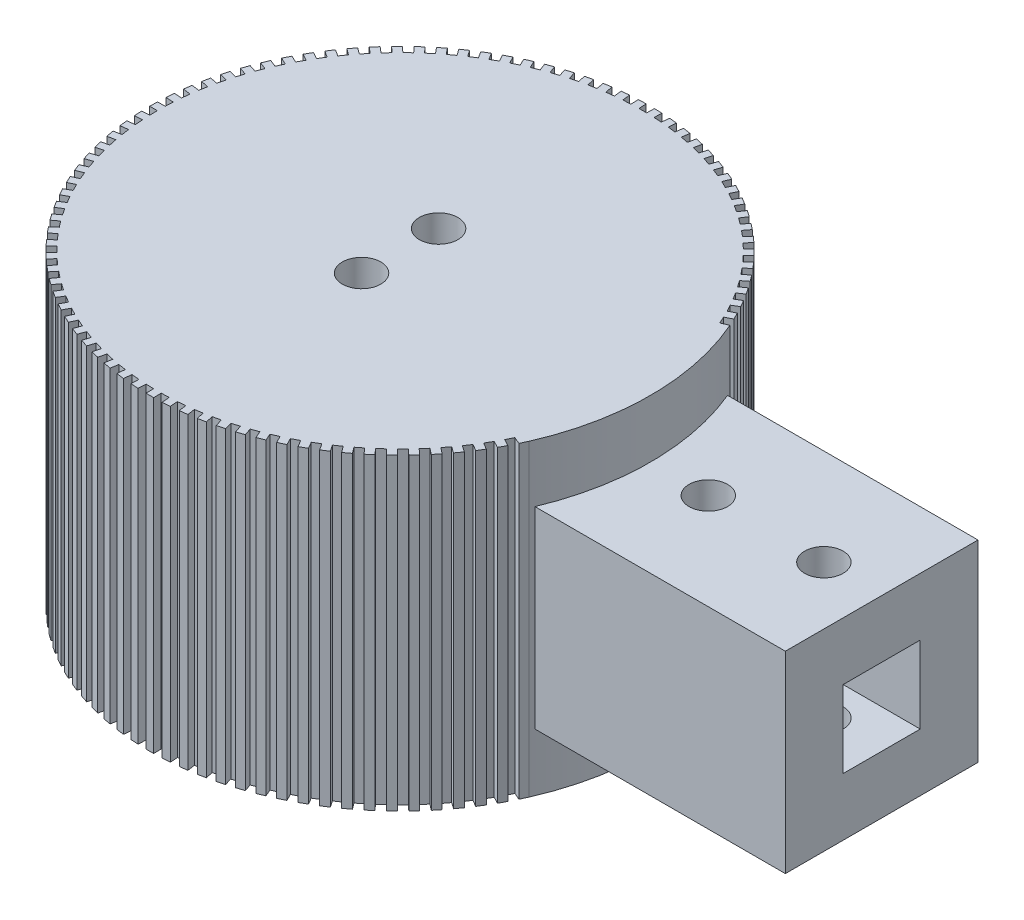
SolidWorks part; units mm, degrees
ref_plane "Front Plane" through (0, 0, 0) normal (0, 0, 1) x (1, 0, 0)
ref_plane "Top Plane" through (0, 0, 0) normal (0, 1, 0) x (1, 0, 0)
ref_plane "Right Plane" through (0, 0, 0) normal (1, 0, 0) x (0, 0, -1)
sketch "Sketch1" plane through (0, 0, 0) normal (0, 1, 0) x (1, 0, 0)
  circle A0 centre (0, 0) radius 32.5
  dimension "D1" = 65
extrude "Boss-Extrude1" add sketch "Sketch1" along normal blind 40
sketch "Sketch2" plane through (0, 0, 0) normal (1, 0, 0) x (0, 0, -1)
  line L0 (0, 0) -> (0, 40) construction
  line L1 (32.5, 40) -> (-32.5, 40) construction
  line L2 (12.5, 20) -> (-12.5, 20) construction
  line L3 (0, 32.5) -> (0, 7.5) construction
  line L4 (0, 32.5) -> (-12.5, 32.5)
  line L5 (-12.5, 32.5) -> (-12.5, 7.5)
  line L6 (-12.5, 7.5) -> (12.5, 7.5)
  line L7 (12.5, 7.5) -> (12.5, 32.5)
  line L8 (12.5, 32.5) -> (0, 32.5)
  line L10 (5, 15) -> (-5, 15)
  line L11 (5, 15) -> (5, 25)
  line L12 (5, 25) -> (-5, 25)
  line L13 (-5, 15) -> (-5, 25)
  line L14 (5, 15) -> (-5, 25) construction
  line L15 (5, 25) -> (-5, 15) construction
  point P8 (0, 20)
  point P11 (0, 20)
  point P15 (0, 20)
  dimension "D1" = 25
  dimension "D2" = 25
  dimension "D3" = 10
  dimension "D4" = 10
extrude "Boss-Extrude2" add sketch "Sketch2" along normal blind 62.5
sketch "Sketch3" plane through (0, 40, 0) normal (0, 1, 0) x (1, 0, 0)
  line L0 (0, -5) -> (0, 5) construction
  circle A0 centre (0, 5) radius 2.5
  circle A1 centre (0, -5) radius 2.5
  point P4 (0, 0)
  dimension "D2" = 5
  dimension "D3" = 5
  dimension "D1" = 10
extrude "Cut-Extrude1" cut sketch "Sketch3" against normal through all both and the other way through all
sketch "Sketch4" plane through (0, 32.5, 0) normal (0, 1, 0) x (1, 0, 0)
  line L1 (62.5, 12.5) -> (62.5, -12.5) construction
  line L2 (32.5, 0) -> (47.5, 0) construction
  line L3 (47.5, 0) -> (62.5, 0) construction
  arc A0 (30, -12.5) -> (30, 12.5) centre (0, 0) ccw construction
  circle A1 centre (40, 0) radius 2.5
  circle A2 centre (55, 0) radius 2.5
  dimension "D1" = 5
  dimension "D2" = 5
extrude "Cut-Extrude2" cut sketch "Sketch4" against normal through all both and the other way through all
sketch "Sketch5" plane through (0, 40, 0) normal (0, 1, 0) x (1, 0, 0)
  line L0 (-31.5, 0) -> (-32.4949, 0)
  line L1 (-32.4949, 0) -> (-32.4795, 1)
  line L2 (-32.4795, 1) -> (-31.4841, 1)
  line L3 (-31.4366, 1.9979) -> (-32.4294, 2.061)
  line L4 (-32.4294, 2.061) -> (-32.3507, 3.058)
  line L5 (-32.3507, 3.058) -> (-31.3573, 2.9948)
  line L6 (-31.2466, 3.9877) -> (-32.2334, 4.1136)
  line L7 (-32.2334, 4.1136) -> (-32.0916, 5.1036)
  line L8 (-32.0916, 5.1036) -> (-31.1042, 4.9776)
  line L9 (-30.9308, 5.9614) -> (-31.9076, 6.1497)
  line L10 (-31.9076, 6.1497) -> (-31.7033, 7.1287)
  line L11 (-31.7033, 7.1287) -> (-30.7259, 6.9403)
  line L12 (-30.4904, 7.9112) -> (-31.4534, 8.161)
  line L13 (-31.4534, 8.161) -> (-31.1873, 9.1251)
  line L14 (-31.1873, 9.1251) -> (-30.2239, 8.8751)
  line L15 (-29.9272, 9.8291) -> (-30.8724, 10.1395)
  line L16 (-30.8724, 10.1395) -> (-30.5458, 11.0848)
  line L17 (-30.5458, 11.0848) -> (-29.6001, 10.7742)
  line L18 (-29.2436, 11.7074) -> (-30.1672, 12.0771)
  line L19 (-30.1672, 12.0771) -> (-29.7812, 12.9998)
  line L20 (-29.7812, 12.9998) -> (-28.8572, 12.6298)
  line L21 (-28.4422, 13.5385) -> (-29.3405, 13.9661)
  line L22 (-29.3405, 13.9661) -> (-28.8968, 14.8624)
  line L23 (-28.8968, 14.8624) -> (-27.9981, 14.4346)
  line L24 (-27.5263, 15.3152) -> (-28.3956, 15.7989)
  line L25 (-28.3956, 15.7989) -> (-27.896, 16.6653)
  line L26 (-27.896, 16.6653) -> (-27.0262, 16.1813)
  line L27 (-26.4995, 17.0302) -> (-27.3364, 17.5681)
  line L28 (-27.3364, 17.5681) -> (-26.7828, 18.401)
  line L29 (-26.7828, 18.401) -> (-25.9455, 17.8629)
  line L30 (-25.366, 18.6766) -> (-26.1671, 19.2665)
  line L31 (-26.1671, 19.2665) -> (-25.5618, 20.0626)
  line L32 (-25.5618, 20.0626) -> (-24.7603, 19.4725)
  line L33 (-24.1304, 20.2478) -> (-24.8925, 20.8873)
  line L34 (-24.8925, 20.8873) -> (-24.2379, 21.6434)
  line L35 (-24.2379, 21.6434) -> (-23.4754, 21.0036)
  line L36 (-22.7976, 21.7375) -> (-23.5176, 22.424)
  line L37 (-23.5176, 22.424) -> (-22.8164, 23.1371)
  line L38 (-22.8164, 23.1371) -> (-22.0961, 22.4503)
  line L39 (-21.373, 23.1396) -> (-22.0481, 23.8705)
  line L40 (-22.0481, 23.8705) -> (-21.303, 24.5377)
  line L41 (-21.303, 24.5377) -> (-20.6277, 23.8065)
  line L42 (-19.8624, 24.4486) -> (-20.4897, 25.2208)
  line L43 (-20.4897, 25.2208) -> (-19.7039, 25.8394)
  line L44 (-19.7039, 25.8394) -> (-19.0763, 25.0668)
  line L45 (-18.2718, 25.6591) -> (-18.8489, 26.4695)
  line L46 (-18.8489, 26.4695) -> (-18.0254, 27.0371)
  line L47 (-18.0254, 27.0371) -> (-17.448, 26.2263)
  line L48 (-16.6076, 26.7664) -> (-17.1321, 27.6117)
  line L49 (-17.1321, 27.6117) -> (-16.2743, 28.1259)
  line L50 (-16.2743, 28.1259) -> (-15.7495, 27.2801)
  line L51 (-14.8765, 27.7658) -> (-15.3464, 28.6427)
  line L52 (-15.3464, 28.6427) -> (-14.4577, 29.1014)
  line L53 (-14.4577, 29.1014) -> (-13.9876, 28.2241)
  line L54 (-13.0856, 28.6534) -> (-13.4989, 29.5584)
  line L55 (-13.4989, 29.5584) -> (-12.5828, 29.9598)
  line L56 (-12.5828, 29.9598) -> (-12.1693, 29.0544)
  line L57 (-11.2419, 29.4257) -> (-11.597, 30.355)
  line L58 (-11.597, 30.355) -> (-10.6573, 30.6975)
  line L59 (-10.6573, 30.6975) -> (-10.3021, 29.7677)
  line L60 (-9.353, 30.0794) -> (-9.6484, 31.0294)
  line L61 (-9.6484, 31.0294) -> (-8.6889, 31.3116)
  line L62 (-8.6889, 31.3116) -> (-8.3934, 30.3612)
  line L63 (-7.4264, 30.6121) -> (-7.661, 31.5789)
  line L64 (-7.661, 31.5789) -> (-6.6855, 31.7997)
  line L65 (-6.6855, 31.7997) -> (-6.4509, 30.8324)
  line L66 (-5.4699, 31.0214) -> (-5.6427, 32.0012)
  line L67 (-5.6427, 32.0012) -> (-4.6552, 32.1597)
  line L68 (-4.6552, 32.1597) -> (-4.4824, 31.1795)
  line L69 (-3.4914, 31.3059) -> (-3.6017, 32.2946)
  line L70 (-3.6017, 32.2946) -> (-2.6061, 32.3902)
  line L71 (-2.6061, 32.3902) -> (-2.4958, 31.401)
  line L72 (-1.4988, 31.4643) -> (-1.5462, 32.4581)
  line L73 (-1.5462, 32.4581) -> (-0.5466, 32.4903)
  line L74 (-0.5466, 32.4903) -> (-0.4992, 31.496)
  line L75 (0.4998, 31.496) -> (0.5156, 32.4908)
  line L76 (0.5156, 32.4908) -> (1.5152, 32.4595)
  line L77 (1.5152, 32.4595) -> (1.4994, 31.4643)
  line L78 (2.4964, 31.4009) -> (2.5752, 32.3927)
  line L79 (2.5752, 32.3927) -> (3.5709, 32.2981)
  line L80 (3.5709, 32.2981) -> (3.492, 31.3058)
  line L81 (4.4829, 31.1794) -> (4.6245, 32.1641)
  line L82 (4.6245, 32.1641) -> (5.6121, 32.0066)
  line L83 (5.6121, 32.0066) -> (5.4705, 31.0213)
  line L84 (6.4514, 30.8323) -> (6.6552, 31.8061)
  line L85 (6.6552, 31.8061) -> (7.6308, 31.5862)
  line L86 (7.6308, 31.5862) -> (7.427, 30.6119)
  line L87 (8.3939, 30.361) -> (8.659, 31.3199)
  line L88 (8.659, 31.3199) -> (9.6188, 31.0386)
  line L89 (9.6188, 31.0386) -> (9.3535, 30.0793)
  line L90 (10.3026, 29.7675) -> (10.628, 30.7077)
  line L91 (10.628, 30.7077) -> (11.568, 30.3661)
  line L92 (11.568, 30.3661) -> (11.2424, 29.4255)
  line L93 (12.1699, 29.0542) -> (12.5542, 29.9718)
  line L94 (12.5542, 29.9718) -> (13.4706, 29.5712)
  line L95 (13.4706, 29.5712) -> (13.0861, 28.6532)
  line L96 (13.9881, 28.2238) -> (14.4299, 29.1152)
  line L97 (14.4299, 29.1152) -> (15.319, 28.6573)
  line L98 (15.319, 28.6573) -> (14.877, 27.7655)
  line L99 (15.75, 27.2798) -> (16.2474, 28.1414)
  line L100 (16.2474, 28.1414) -> (17.1058, 27.6281)
  line L101 (17.1058, 27.6281) -> (16.6081, 26.7661)
  line L102 (17.4485, 26.226) -> (17.9996, 27.0542)
  line L103 (17.9996, 27.0542) -> (18.8236, 26.4875)
  line L104 (18.8236, 26.4875) -> (18.2723, 25.6588)
  line L105 (19.0767, 25.0665) -> (19.6792, 25.8582)
  line L106 (19.6792, 25.8582) -> (20.4656, 25.2403)
  line L107 (20.4656, 25.2403) -> (19.8629, 24.4483)
  line L108 (20.6281, 23.8061) -> (21.2796, 24.558)
  line L109 (21.2796, 24.558) -> (22.0253, 23.8915)
  line L110 (22.0253, 23.8915) -> (21.3735, 23.1393)
  line L111 (22.0965, 22.4499) -> (22.7943, 23.1589)
  line L112 (22.7943, 23.1589) -> (23.4962, 22.4465)
  line L113 (23.4962, 22.4465) -> (22.798, 21.7371)
  line L114 (23.4758, 21.0032) -> (24.2173, 21.6666)
  line L115 (24.2173, 21.6666) -> (24.8726, 20.911)
  line L116 (24.8726, 20.911) -> (24.1308, 20.2474)
  line L117 (24.7607, 19.472) -> (25.5427, 20.087)
  line L118 (25.5427, 20.087) -> (26.1488, 19.2914)
  line L119 (26.1488, 19.2914) -> (25.3664, 18.6761)
  line L120 (25.9458, 17.8624) -> (26.7653, 18.4265)
  line L121 (26.7653, 18.4265) -> (27.3196, 17.5941)
  line L122 (27.3196, 17.5941) -> (26.4998, 17.0297)
  line L123 (27.0265, 16.1808) -> (27.8801, 16.6919)
  line L124 (27.8801, 16.6919) -> (28.3805, 15.826)
  line L125 (28.3805, 15.826) -> (27.5265, 15.3147)
  line L126 (27.9983, 14.4341) -> (28.8826, 14.89)
  line L127 (28.8826, 14.89) -> (29.3271, 13.9941)
  line L128 (29.3271, 13.9941) -> (28.4424, 13.538)
  line L129 (28.8574, 12.6293) -> (29.7688, 13.0282)
  line L169 (29.7688, -13.0282) -> (29.3538, -13.9381)
  line L170 (29.3538, -13.9381) -> (28.4419, -13.5391)
  line L171 (27.9983, -14.4341) -> (28.8826, -14.89)
  line L172 (28.8826, -14.89) -> (28.4107, -15.7718)
  line L173 (28.4107, -15.7718) -> (27.526, -15.3157)
  line L174 (27.0265, -16.1808) -> (27.8801, -16.6919)
  line L175 (27.8801, -16.6919) -> (27.3532, -17.542)
  line L176 (27.3532, -17.542) -> (26.4992, -17.0307)
  line L177 (25.9458, -17.8624) -> (26.7653, -18.4265)
  line L178 (26.7653, -18.4265) -> (26.1855, -19.2415)
  line L179 (26.1855, -19.2415) -> (25.3657, -18.6771)
  line L180 (24.7607, -19.472) -> (25.5427, -20.087)
  line L181 (25.5427, -20.087) -> (24.9124, -20.8635)
  line L182 (24.9124, -20.8635) -> (24.13, -20.2482)
  line L183 (23.4758, -21.0032) -> (24.2173, -21.6666)
  line L184 (24.2173, -21.6666) -> (23.539, -22.4016)
  line L185 (23.539, -22.4016) -> (22.7972, -21.7379)
  line L186 (22.0965, -22.4499) -> (22.7943, -23.1589)
  line L187 (22.7943, -23.1589) -> (22.0708, -23.8494)
  line L188 (22.0708, -23.8494) -> (21.3726, -23.14)
  line L189 (20.6281, -23.8061) -> (21.2796, -24.558)
  line L190 (21.2796, -24.558) -> (20.5138, -25.2012)
  line L191 (20.5138, -25.2012) -> (19.862, -24.449)
  line L192 (19.0767, -25.0665) -> (19.6792, -25.8582)
  line L193 (19.6792, -25.8582) -> (18.8741, -26.4515)
  line L194 (18.8741, -26.4515) -> (18.2713, -25.6595)
  line L195 (17.4485, -26.226) -> (17.9996, -27.0542)
  line L196 (17.9996, -27.0542) -> (17.1585, -27.5954)
  line L197 (17.1585, -27.5954) -> (16.6071, -26.7667)
  line L198 (15.75, -27.2798) -> (16.2474, -28.1414)
  line L199 (16.2474, -28.1414) -> (15.3737, -28.6281)
  line L200 (15.3737, -28.6281) -> (14.876, -27.7661)
  line L201 (13.9881, -28.2238) -> (14.4299, -29.1152)
  line L202 (14.4299, -29.1152) -> (13.5271, -29.5455)
  line L203 (13.5271, -29.5455) -> (13.0851, -28.6536)
  line L204 (12.1699, -29.0542) -> (12.5542, -29.9718)
  line L205 (12.5542, -29.9718) -> (11.6259, -30.3439)
  line L206 (11.6259, -30.3439) -> (11.2414, -29.4259)
  line L207 (10.3026, -29.7675) -> (10.628, -30.7077)
  line L208 (10.628, -30.7077) -> (9.678, -31.0202)
  line L209 (9.678, -31.0202) -> (9.3524, -30.0796)
  line L210 (8.3939, -30.361) -> (8.659, -31.3199)
  line L211 (8.659, -31.3199) -> (7.6911, -31.5716)
  line L212 (7.6911, -31.5716) -> (7.4259, -30.6122)
  line L213 (6.4514, -30.8323) -> (6.6552, -31.8061)
  line L214 (6.6552, -31.8061) -> (5.6732, -31.9958)
  line L215 (5.6732, -31.9958) -> (5.4694, -31.0215)
  line L216 (4.4829, -31.1794) -> (4.6245, -32.1641)
  line L217 (4.6245, -32.1641) -> (3.6325, -32.2912)
  line L218 (3.6325, -32.2912) -> (3.4908, -31.306)
  line L219 (2.4964, -31.4009) -> (2.5752, -32.3927)
  line L220 (2.5752, -32.3927) -> (1.5771, -32.4566)
  line L221 (1.5771, -32.4566) -> (1.4983, -31.4643)
  line L222 (0.4998, -31.496) -> (0.5156, -32.4908)
  line L223 (0.5156, -32.4908) -> (-0.4846, -32.4913)
  line L224 (-0.4846, -32.4913) -> (-0.5003, -31.496)
  line L225 (-1.4988, -31.4643) -> (-1.5462, -32.4581)
  line L226 (-1.5462, -32.4581) -> (-2.5443, -32.3951)
  line L227 (-2.5443, -32.3951) -> (-2.4969, -31.4009)
  line L228 (-3.4914, -31.3059) -> (-3.6017, -32.2946)
  line L229 (-3.6017, -32.2946) -> (-4.5938, -32.1685)
  line L230 (-4.5938, -32.1685) -> (-4.4835, -31.1793)
  line L231 (-5.4699, -31.0214) -> (-5.6427, -32.0012)
  line L232 (-5.6427, -32.0012) -> (-6.6248, -31.8124)
  line L233 (-6.6248, -31.8124) -> (-6.452, -30.8322)
  line L234 (-7.4264, -30.6121) -> (-7.661, -31.5789)
  line L235 (-7.661, -31.5789) -> (-8.6291, -31.3282)
  line L236 (-8.6291, -31.3282) -> (-8.3945, -30.3609)
  line L237 (-9.353, -30.0794) -> (-9.6484, -31.0294)
  line L238 (-9.6484, -31.0294) -> (-10.5987, -30.7178)
  line L239 (-10.5987, -30.7178) -> (-10.3032, -29.7673)
  line L240 (-11.2419, -29.4257) -> (-11.597, -30.355)
  line L241 (-11.597, -30.355) -> (-12.5256, -29.9837)
  line L242 (-12.5256, -29.9837) -> (-12.1704, -29.0539)
  line L243 (-13.0856, -28.6534) -> (-13.4989, -29.5584)
  line L244 (-13.4989, -29.5584) -> (-14.4021, -29.129)
  line L245 (-14.4021, -29.129) -> (-13.9886, -28.2236)
  line L246 (-14.8765, -27.7658) -> (-15.3464, -28.6427)
  line L247 (-15.3464, -28.6427) -> (-16.2206, -28.1569)
  line L248 (-16.2206, -28.1569) -> (-15.7505, -27.2795)
  line L249 (-16.6076, -26.7664) -> (-17.1321, -27.6117)
  line L250 (-17.1321, -27.6117) -> (-17.9737, -27.0714)
  line L251 (-17.9737, -27.0714) -> (-17.449, -26.2256)
  line L252 (-18.2718, -25.6591) -> (-18.8489, -26.4695)
  line L253 (-18.8489, -26.4695) -> (-19.6545, -25.8769)
  line L254 (-19.6545, -25.8769) -> (-19.0772, -25.0662)
  line L255 (-19.8624, -24.4486) -> (-20.4897, -25.2208)
  line L256 (-20.4897, -25.2208) -> (-21.2562, -24.5783)
  line L257 (-21.2562, -24.5783) -> (-20.6285, -23.8057)
  line L258 (-21.373, -23.1396) -> (-22.0481, -23.8705)
  line L259 (-22.0481, -23.8705) -> (-22.7722, -23.1806)
  line L260 (-22.7722, -23.1806) -> (-22.0969, -22.4495)
  line L261 (-22.7976, -21.7375) -> (-23.5176, -22.424)
  line L262 (-23.5176, -22.424) -> (-24.1966, -21.6897)
  line L263 (-24.1966, -21.6897) -> (-23.4762, -21.0028)
  line L264 (-24.1304, -20.2478) -> (-24.8925, -20.8873)
  line L265 (-24.8925, -20.8873) -> (-25.5235, -20.1114)
  line L266 (-25.5235, -20.1114) -> (-24.761, -19.4716)
  line L267 (-25.366, -18.6766) -> (-26.1671, -19.2665)
  line L268 (-26.1671, -19.2665) -> (-26.7477, -18.4521)
  line L269 (-26.7477, -18.4521) -> (-25.9461, -17.8619)
  line L270 (-26.4995, -17.0302) -> (-27.3364, -17.5681)
  line L271 (-27.3364, -17.5681) -> (-27.8641, -16.7185)
  line L272 (-27.8641, -16.7185) -> (-27.0268, -16.1803)
  line L273 (-27.5263, -15.3152) -> (-28.3956, -15.7989)
  line L274 (-28.3956, -15.7989) -> (-28.8684, -14.9176)
  line L275 (-28.8684, -14.9176) -> (-27.9986, -14.4336)
  line L276 (-28.4422, -13.5385) -> (-29.3405, -13.9661)
  line L277 (-29.3405, -13.9661) -> (-29.7564, -13.0566)
  line L278 (-29.7564, -13.0566) -> (-28.8576, -12.6288)
  line L279 (-29.2436, -11.7074) -> (-30.1672, -12.0771)
  line L280 (-30.1672, -12.0771) -> (-30.5246, -11.143)
  line L281 (-30.5246, -11.143) -> (-29.6005, -10.7731)
  line L282 (-29.9272, -9.8291) -> (-30.8724, -10.1395)
  line L283 (-30.8724, -10.1395) -> (-31.1698, -9.1846)
  line L284 (-31.1698, -9.1846) -> (-30.2242, -8.874)
  line L285 (-30.4904, -7.9112) -> (-31.4534, -8.161)
  line L286 (-31.4534, -8.161) -> (-31.6896, -7.1892)
  line L287 (-31.6896, -7.1892) -> (-30.7262, -6.9392)
  line L288 (-30.9308, -5.9614) -> (-31.9076, -6.1497)
  line L289 (-31.9076, -6.1497) -> (-32.0818, -5.1649)
  line L290 (-32.0818, -5.1649) -> (-31.1044, -4.9765)
  line L291 (-31.2466, -3.9877) -> (-32.2334, -4.1136)
  line L292 (-32.2334, -4.1136) -> (-32.3448, -3.1197)
  line L293 (-32.3448, -3.1197) -> (-31.3574, -2.9937)
  line L294 (-31.4366, -1.9979) -> (-32.4294, -2.061)
  line L295 (-32.4294, -2.061) -> (-32.4775, -1.062)
  line L296 (-32.4775, -1.062) -> (-31.4842, -0.9989)
  line L297 (-31.4841, 1) -> (-31.4366, 1.9979)
  line L298 (-31.3573, 2.9948) -> (-31.2466, 3.9877)
  line L299 (-31.1042, 4.9776) -> (-30.9308, 5.9614)
  line L300 (-30.7259, 6.9403) -> (-30.4904, 7.9112)
  line L301 (-30.2239, 8.8751) -> (-29.9272, 9.8291)
  line L302 (-29.6001, 10.7742) -> (-29.2436, 11.7074)
  line L303 (-28.8572, 12.6298) -> (-28.4422, 13.5385)
  line L304 (-27.9981, 14.4346) -> (-27.5263, 15.3152)
  line L305 (-27.0262, 16.1813) -> (-26.4995, 17.0302)
  line L306 (-25.9455, 17.8629) -> (-25.366, 18.6766)
  line L307 (-24.7603, 19.4725) -> (-24.1304, 20.2478)
  line L308 (-23.4754, 21.0036) -> (-22.7976, 21.7375)
  line L309 (-22.0961, 22.4503) -> (-21.373, 23.1396)
  line L310 (-20.6277, 23.8065) -> (-19.8624, 24.4486)
  line L311 (-19.0763, 25.0668) -> (-18.2718, 25.6591)
  line L312 (-17.448, 26.2263) -> (-16.6076, 26.7664)
  line L313 (-15.7495, 27.2801) -> (-14.8765, 27.7658)
  line L314 (-13.9876, 28.2241) -> (-13.0856, 28.6534)
  line L315 (-12.1693, 29.0544) -> (-11.2419, 29.4257)
  line L316 (-10.3021, 29.7677) -> (-9.353, 30.0794)
  line L317 (-8.3934, 30.3612) -> (-7.4264, 30.6121)
  line L318 (-6.4509, 30.8324) -> (-5.4699, 31.0214)
  line L319 (-4.4824, 31.1795) -> (-3.4914, 31.3059)
  line L320 (-2.4958, 31.401) -> (-1.4988, 31.4643)
  line L321 (-0.4992, 31.496) -> (0.4998, 31.496)
  line L322 (1.4994, 31.4643) -> (2.4964, 31.4009)
  line L323 (3.492, 31.3058) -> (4.4829, 31.1794)
  line L324 (5.4705, 31.0213) -> (6.4514, 30.8323)
  line L325 (7.427, 30.6119) -> (8.3939, 30.361)
  line L326 (9.3535, 30.0793) -> (10.3026, 29.7675)
  line L327 (11.2424, 29.4255) -> (12.1699, 29.0542)
  line L328 (13.0861, 28.6532) -> (13.9881, 28.2238)
  line L329 (14.877, 27.7655) -> (15.75, 27.2798)
  line L330 (16.6081, 26.7661) -> (17.4485, 26.226)
  line L331 (18.2723, 25.6588) -> (19.0767, 25.0665)
  line L332 (19.8629, 24.4483) -> (20.6281, 23.8061)
  line L333 (21.3735, 23.1393) -> (22.0965, 22.4499)
  line L334 (22.798, 21.7371) -> (23.4758, 21.0032)
  line L335 (24.1308, 20.2474) -> (24.7607, 19.472)
  line L336 (25.3664, 18.6761) -> (25.9458, 17.8624)
  line L337 (26.4998, 17.0297) -> (27.0265, 16.1808)
  line L338 (27.5265, 15.3147) -> (27.9983, 14.4341)
  line L339 (28.4424, 13.538) -> (28.8574, 12.6293)
  line L353 (28.4419, -13.5391) -> (27.9983, -14.4341)
  line L354 (27.526, -15.3157) -> (27.0265, -16.1808)
  line L355 (26.4992, -17.0307) -> (25.9458, -17.8624)
  line L356 (25.3657, -18.6771) -> (24.7607, -19.472)
  line L357 (24.13, -20.2482) -> (23.4758, -21.0032)
  line L358 (22.7972, -21.7379) -> (22.0965, -22.4499)
  line L359 (21.3726, -23.14) -> (20.6281, -23.8061)
  line L360 (19.862, -24.449) -> (19.0767, -25.0665)
  line L361 (18.2713, -25.6595) -> (17.4485, -26.226)
  line L362 (16.6071, -26.7667) -> (15.75, -27.2798)
  line L363 (14.876, -27.7661) -> (13.9881, -28.2238)
  line L364 (13.0851, -28.6536) -> (12.1699, -29.0542)
  line L365 (11.2414, -29.4259) -> (10.3026, -29.7675)
  line L366 (9.3524, -30.0796) -> (8.3939, -30.361)
  line L367 (7.4259, -30.6122) -> (6.4514, -30.8323)
  line L368 (5.4694, -31.0215) -> (4.4829, -31.1794)
  line L369 (3.4908, -31.306) -> (2.4964, -31.4009)
  line L370 (1.4983, -31.4643) -> (0.4998, -31.496)
  line L371 (-0.5003, -31.496) -> (-1.4988, -31.4643)
  line L372 (-2.4969, -31.4009) -> (-3.4914, -31.3059)
  line L373 (-4.4835, -31.1793) -> (-5.4699, -31.0214)
  line L374 (-6.452, -30.8322) -> (-7.4264, -30.6121)
  line L375 (-8.3945, -30.3609) -> (-9.353, -30.0794)
  line L376 (-10.3032, -29.7673) -> (-11.2419, -29.4257)
  line L377 (-12.1704, -29.0539) -> (-13.0856, -28.6534)
  line L378 (-13.9886, -28.2236) -> (-14.8765, -27.7658)
  line L379 (-15.7505, -27.2795) -> (-16.6076, -26.7664)
  line L380 (-17.449, -26.2256) -> (-18.2718, -25.6591)
  line L381 (-19.0772, -25.0662) -> (-19.8624, -24.4486)
  line L382 (-20.6285, -23.8057) -> (-21.373, -23.1396)
  line L383 (-22.0969, -22.4495) -> (-22.7976, -21.7375)
  line L384 (-23.4762, -21.0028) -> (-24.1304, -20.2478)
  line L385 (-24.761, -19.4716) -> (-25.366, -18.6766)
  line L386 (-25.9461, -17.8619) -> (-26.4995, -17.0302)
  line L387 (-27.0268, -16.1803) -> (-27.5263, -15.3152)
  line L388 (-27.9986, -14.4336) -> (-28.4422, -13.5385)
  line L389 (-28.8576, -12.6288) -> (-29.2436, -11.7074)
  line L390 (-29.6005, -10.7731) -> (-29.9272, -9.8291)
  line L391 (-30.2242, -8.874) -> (-30.4904, -7.9112)
  line L392 (-30.7262, -6.9392) -> (-30.9308, -5.9614)
  line L393 (-31.1044, -4.9765) -> (-31.2466, -3.9877)
  line L394 (-31.3574, -2.9937) -> (-31.4366, -1.9979)
  line L395 (-31.4842, -0.9989) -> (-31.5, 0)
  line L396 (29.7688, 13.0282) -> (34.6958, 15.1845)
  line L397 (29.7688, -13.0282) -> (34.6958, -15.1845)
  line L399 (29.7688, 13.0282) -> (30.1557, 12.1059) [skipped]
  line L400 (30.1557, 12.1059) -> (29.2438, 11.7068) [skipped]
  line L401 (29.6003, 10.7736) -> (30.5352, 11.1139) [skipped]
  line L402 (30.5352, 11.1139) -> (30.8627, 10.1689) [skipped]
  line L403 (30.8627, 10.1689) -> (29.9274, 9.8285) [skipped]
  line L404 (30.224, 8.8746) -> (31.1786, 9.1549) [skipped]
  line L405 (31.1786, 9.1549) -> (31.4456, 8.191) [skipped]
  line L406 (31.4456, 8.191) -> (30.4905, 7.9106) [skipped]
  line L407 (30.726, 6.9398) -> (31.6965, 7.159) [skipped]
  line L408 (31.6965, 7.159) -> (31.9018, 6.1801) [skipped]
  line L409 (31.9018, 6.1801) -> (30.9309, 5.9609) [skipped]
  line L410 (31.1043, 4.977) -> (32.0867, 5.1342) [skipped]
  line L411 (32.0867, 5.1342) -> (32.2295, 4.1444) [skipped]
  line L412 (32.2295, 4.1444) -> (31.2466, 3.9871) [skipped]
  line L413 (31.3574, 2.9943) -> (32.3477, 3.0888) [skipped]
  line L414 (32.3477, 3.0888) -> (32.4275, 2.0919) [skipped]
  line L415 (32.4275, 2.0919) -> (31.4366, 1.9973) [skipped]
  line L416 (31.4841, 0.9994) -> (32.4785, 1.031) [skipped]
  line L417 (32.4785, 1.031) -> (32.4949, 0.031) [skipped]
  line L418 (32.4949, 0.031) -> (31.5, -0.0006) [skipped]
  line L419 (31.4841, -0.9994) -> (32.4785, -1.031) [skipped]
  line L420 (32.4785, -1.031) -> (32.4314, -2.03) [skipped]
  line L421 (32.4314, -2.03) -> (31.4365, -1.9984) [skipped]
  line L422 (31.3574, -2.9943) -> (32.3477, -3.0888) [skipped]
  line L423 (32.3477, -3.0888) -> (32.2373, -4.0828) [skipped]
  line L424 (32.2373, -4.0828) -> (31.2465, -3.9882) [skipped]
  line L425 (31.1043, -4.977) -> (32.0867, -5.1342) [skipped]
  line L426 (32.0867, -5.1342) -> (31.9135, -6.1192) [skipped]
  line L427 (31.9135, -6.1192) -> (30.9306, -5.962) [skipped]
  line L428 (30.726, -6.9398) -> (31.6965, -7.159) [skipped]
  line L429 (31.6965, -7.159) -> (31.4611, -8.131) [skipped]
  line L430 (31.4611, -8.131) -> (30.4902, -7.9117) [skipped]
  line L431 (30.224, -8.8746) -> (31.1786, -9.1549) [skipped]
  line L432 (31.1786, -9.1549) -> (30.8821, -10.11) [skipped]
  line L433 (30.8821, -10.11) -> (29.9271, -9.8296) [skipped]
  line L434 (29.6003, -10.7736) -> (30.5352, -11.1139) [skipped]
  line L435 (30.5352, -11.1139) -> (30.1787, -12.0483) [skipped]
  line L436 (30.1787, -12.0483) -> (29.2434, -11.7079) [skipped]
  line L437 (29.2438, 11.7068) -> (29.6003, 10.7736) [skipped]
  line L438 (29.9274, 9.8285) -> (30.224, 8.8746) [skipped]
  line L439 (30.4905, 7.9106) -> (30.726, 6.9398) [skipped]
  line L440 (30.9309, 5.9609) -> (31.1043, 4.977) [skipped]
  line L441 (31.2466, 3.9871) -> (31.3574, 2.9943) [skipped]
  line L442 (31.4366, 1.9973) -> (31.4841, 0.9994) [skipped]
  line L443 (31.5, -0.0006) -> (31.4841, -0.9994) [skipped]
  line L444 (31.4365, -1.9984) -> (31.3574, -2.9943) [skipped]
  line L445 (31.2465, -3.9882) -> (31.1043, -4.977) [skipped]
  line L446 (30.9306, -5.962) -> (30.726, -6.9398) [skipped]
  line L447 (30.4902, -7.9117) -> (30.224, -8.8746) [skipped]
  line L448 (29.9271, -9.8296) -> (29.6003, -10.7736) [skipped]
  line L449 (29.2434, -11.7079) -> (28.8574, -12.6293) [skipped]
  line L450 (28.8574, -12.6293) -> (29.7688, -13.0282) [skipped]
  arc A2 (34.6958, 15.1845) -> (34.6958, -15.1845) centre (0, 0) ccw
  point P402 (0, 0)
  point P599 (0, 0)
  dimension "D2" = 1
  dimension "D3" = 1
  dimension "D4" = 99
  dimension "D5" = 99
extrude "Cut-Extrude3" cut sketch "Sketch5" against normal through all contours L169 L170 L353 L171 L172 L173 L354 L174 L175 L176 L355 L177 L178 L179 L356 L180 L181 L182 L357 L183 L184 L185 L358 L186 L187 L188 L359 L189 L190 L191 L360 L192 L193 L194 L361 L195 L196 L197 L362 L198 L199 L200 L363 L201 L202 L203 L364 L204 L205 L206 L365 L207 L208 L209 L366 L210 L211 L212 L367 L213 L214 L215 L368 L216 L217 L218 L369 L219 L220 L221 L370 L222 L223 L224 L371 L225 L226 L227 L372 L228 L229 L230 L373 L231 L232 L233 L374 L234 L235 L236 L375 L237 L238 L239 L376 L240 L241 L242 L377 L243 L244 L245 L378 L246 L247 L248 L379 L249 L250 L251 L380 L252 L253 L254 L381 L255 L256 L257 L382 L258 L259 L260 L383 L261 L262 L263 L384 L264 L265 L266 L385 L267 L268 L269 L386 L270 L271 L272 L387 L273 L274 L275 L388 L276 L277 L278 L389 L279 L280 L281 L390 L282 L283 L284 L391 L285 L286 L287 L392 L288 L289 L290 L393 L291 L292 L293 L394 L294 L295 L296 L395 L0 L1 L2 L297 L3 L4 L5 L298 L6 L7 L8 L299 L9 L10 L11 L300 L12 L13 L14 L301 L15 L16 L17 L302 L18 L19 L20 L303 L21 L22 L23 L304 L24 L25 L26 L305 L27 L28 L29 L306 L30 L31 L32 L307 L33 L34 L35 L308 L36 L37 L38 L309 L39 L40 L41 L310 L42 L43 L44 L311 L45 L46 L47 L312 L48 L49 L50 L313 L51 L52 L53 L314 L54 L55 L56 L315 L57 L58 L59 L316 L60 L61 L62 L317 L63 L64 L65 L318 L66 L67 L68 L319 L69 L70 L71 L320 L72 L73 L74 L321 L75 L76 L77 L322 L78 L79 L80 L323 L81 L82 L83 L324 L84 L85 L86 L325 L87 L88 L89 L326 L90 L91 L92 L327 L93 L94 L95 L328 L96 L97 L98 L329 L99 L100 L101 L330 L102 L103 L104 L331 L105 L106 L107 L332 L108 L109 L110 L333 L111 L112 L113 L334 L114 L115 L116 L335 L117 L118 L119 L336 L120 L121 L122 L337 L123 L124 L125 L338 L126 L127 L128 L339 L129 L396 A2 L397
